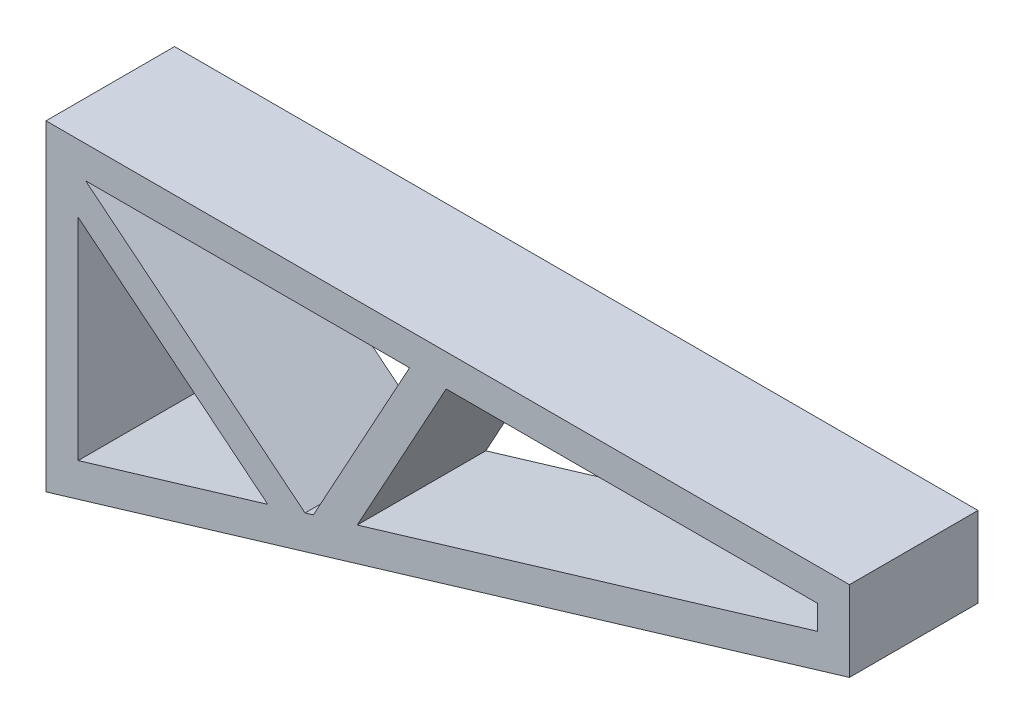
SolidWorks part; units mm, degrees
ref_plane "Alzado" through (0, 0, 0) normal (0, 0, 1) x (1, 0, 0)
ref_plane "Planta" through (0, 0, 0) normal (0, 1, 0) x (1, 0, 0)
ref_plane "Vista lateral" through (0, 0, 0) normal (1, 0, 0) x (0, 0, -1)
sketch "Croquis1" plane through (0, 0, 0) normal (0, 0, 1) x (1, 0, 0)
  line L0 (0, 100) -> (90, 27)
  line L1 (0, 0) -> (250, 75)
  line L2 (0, 0) -> (0, 100)
  line L3 (0, 100) -> (250, 100)
  line L4 (250, 75) -> (250, 100)
  line L5 (90, 27) -> (130, 100)
  line L6 (130, 100) -> (250, 75)
  line L7 (10, 90) -> (240, 90)
  line L8 (240, 82.4403) -> (240, 90)
  line L9 (10, 13.4403) -> (240, 82.4403)
  line L10 (10, 13.4403) -> (10, 90)
  line L11 (128.9694, 90) -> (209.3672, 73.2505)
  line L12 (127.9605, 90.2102) -> (247.9605, 65.2102) construction
  line L13 (83.2001, 35.4003) -> (113.1177, 90)
  line L14 (81.2302, 31.8053) -> (121.2302, 104.8053) construction
  line L15 (10, 79.0129) -> (69.0154, 31.1449)
  line L16 (-6.2994, 92.2336) -> (83.7006, 19.2336) construction
  point P5 (98.0489, 29.4147)
  point P8 (143.1665, 100)
  point P13 (104.6926, 31.4078)
  point P14 (154.0167, 100)
  point P17 (209.6088, 73.323)
  point P20 (130, 90)
  point P23 (112.9635, 90)
  point P26 (83.2988, 35.43)
  point P29 (69.1181, 31.1757)
  point P32 (10, 78.6486)
  dimension "D1" = 250
  dimension "D2" = 100
  dimension "D3" = 25
  dimension "D5" = 120
  dimension "D6" = 90
  dimension "D4" = 10
  dimension "D7" = 10
  dimension "D8" = 10
  dimension "D9" = 10
extrude "Saliente-Extruir1" add sketch "Croquis1" along normal mid plane 40 contours L0 L7 L5 L3 | L9 L10 L7 L0 L2 L1 | L10 L15 L9 L0 L7 | L13 L9 L5 L7 | L9 L0 L5 | L9 L5 L1 L6 | L9 L6 L4 L3 L7 L8 | L5 L7 L6
